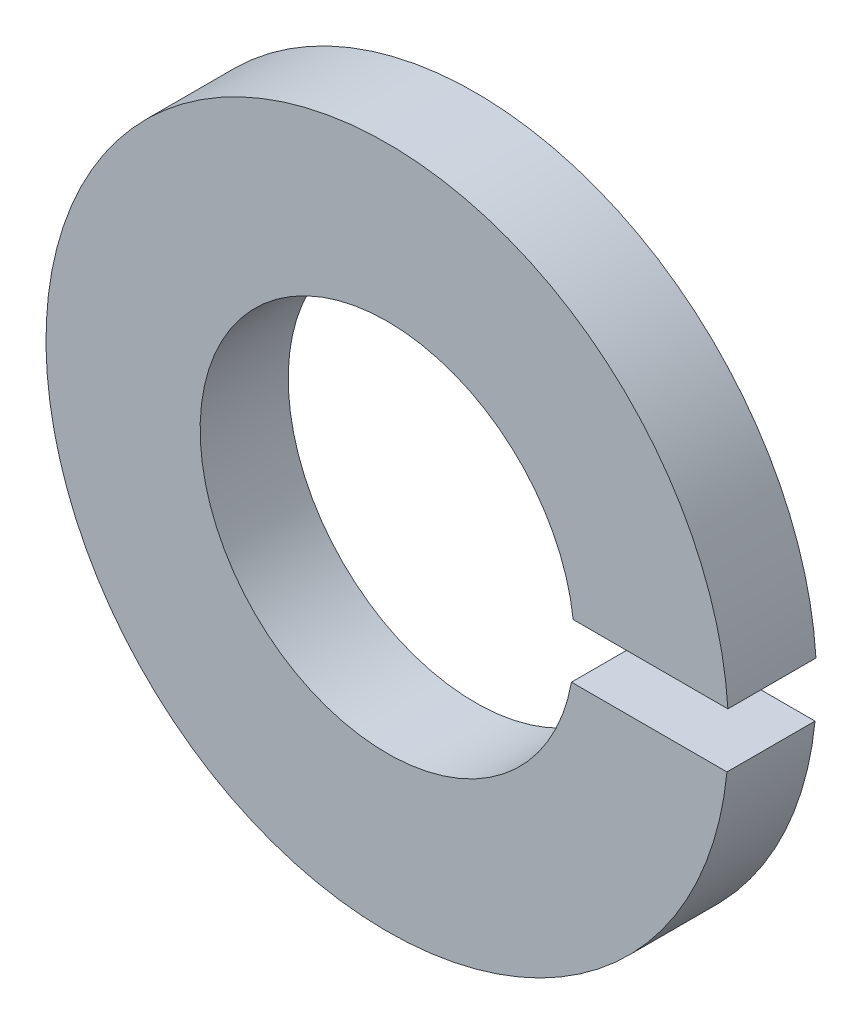
SolidWorks part; units mm, degrees
material "AISI Type A2 Tool Steel"
ref_plane "Front" through (0, 0, 0) normal (0, 0, 1) x (1, 0, 0)
ref_plane "Top" through (0, 0, 0) normal (0, 1, 0) x (1, 0, 0)
ref_plane "Right" through (0, 0, 0) normal (1, 0, 0) x (0, 0, -1)
sketch "Sketch1" plane through (0, 0, 0) normal (0, 0, 1) x (1, 0, 0)
  line L0 (3.3223, -0.3022) -> (0.5645, -0.3022)
  line L1 (3.3223, -0.3022) -> (3.3223, 0.1978)
  line L2 (0.5645, -0.3022) -> (0.5645, 0.1978)
  line L3 (3.3223, 0.1978) -> (0.5645, 0.1978)
  line L4 (3.3223, -0.3022) -> (0.5645, 0.1978) construction
  line L5 (0.5645, -0.3022) -> (3.3223, 0.1978) construction
  arc A0 (3.0937, 0.1978) -> (3.0852, -0.3022) centre (0, 0) ccw
  arc A1 (1.6885, 0.1978) -> (1.6729, -0.3022) centre (0, 0) ccw
  point P5 (1.9434, -0.0522)
  dimension "D1" = 6.2
  dimension "D2" = 3.4
  dimension "D3" = 0.5
extrude "Boss-Extrude1" add sketch "Sketch1" along normal blind 0.8 contours A1 L3 A0 L0
